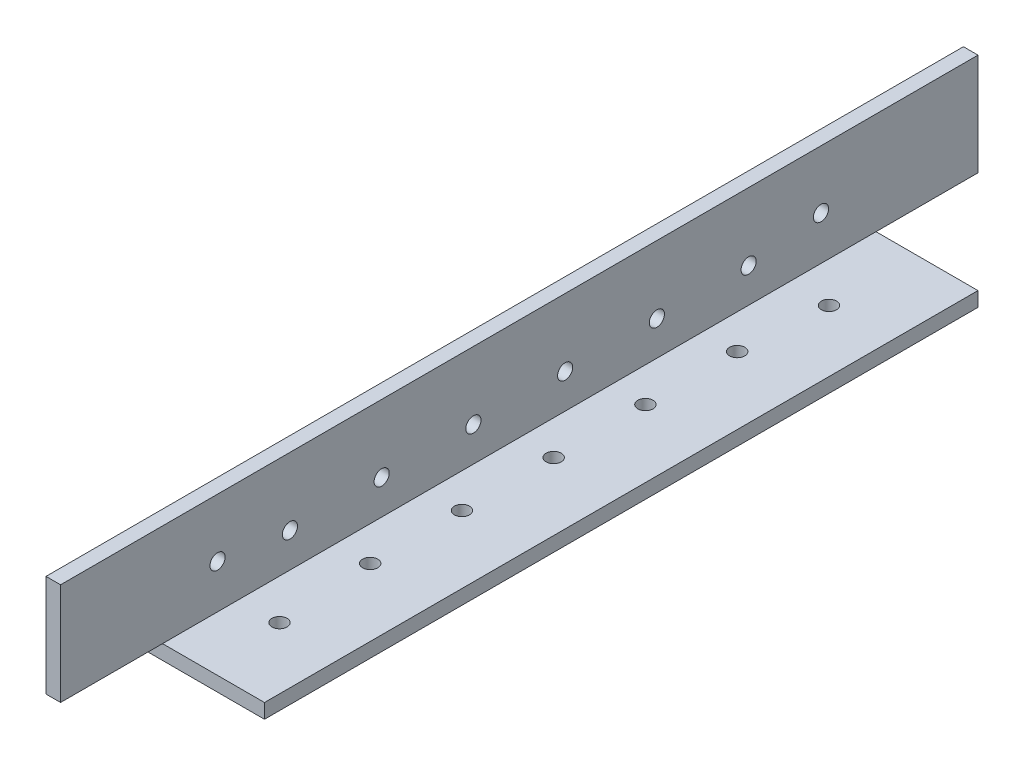
SolidWorks part; units mm, degrees
material "6061-T6 (SS)"
ref_plane "Front Plane" through (0, 0, 0) normal (0, 0, 1) x (1, 0, 0)
ref_plane "Top Plane" through (0, 0, 0) normal (0, 1, 0) x (1, 0, 0)
ref_plane "Right Plane" through (0, 0, 0) normal (1, 0, 0) x (0, 0, -1)
sketch "Sketch1" plane through (0, 0, 0) normal (0, 0, 1) x (1, 0, 0)
  line L0 (0, 25.4) -> (0, 0) construction
  line L1 (0, 0) -> (25.4, 0) construction
  line L2 (25.4, 0) -> (25.4, 3.175) construction
  line L3 (25.4, 3.175) -> (3.175, 3.175) construction
  line L4 (3.175, 3.175) -> (3.175, 25.4) construction
  line L6 (3.175, 25.4) -> (0, 25.4) construction
  arc A0 (3.175, 3.5814) -> (3.5814, 3.175) centre (3.5814, 3.5814) ccw construction
  point P4 (0, 0)
  dimension "Inside Corner Radius" = 0.4064
  dimension "Outside Height" = 25.4
  dimension "Inside Height" = 22.225
  dimension "Outside Width" = 25.4
  dimension "Inside Width" = 22.225
  dimension "Wall Thickness" = 3.175
  dimension "Shape" = 90
sketch "Sketch2" plane through (0, 0, 0) normal (1, 0, 0) x (0, 0, -1)
  line L0 (1219.2, 0) -> (-1219.2, 0) construction
  line L1 (-1219.2, 25.4) -> (-1219.2, 0) construction
  line L2 (1219.2, 25.4) -> (1219.2, 0) construction
  point P0 (-1189.99, 0)
  point P4 (0, 0)
  point P6 (1189.99, 0)
  dimension "D1" = 29.21
  dimension "D2" = 29.21
  dimension "D3" = 25.4
  dimension "Length" = 2438.4
sketch "Sketch3" plane through (0, 0, 0) normal (0, 0, 1) x (1, 0, 0)
  line L0 (3.175, 25.4) -> (0, 25.4)
  line L1 (0, 25.4) -> (0, 0)
  line L2 (0, 0) -> (25.4, 0)
  line L3 (25.4, 0) -> (25.4, 3.175)
  line L4 (25.4, 3.175) -> (3.175, 3.175)
  line L5 (3.175, 3.175) -> (3.175, 25.4)
extrude "Boss-Extrude1" add sketch "Sketch3" along normal mid plane 2438.4
fillet "Fillet1" radius 0.4064 1 edges at (3.175, 3.175, 0)
sketch "Sketch4" plane through (0, 0, 0) normal (-1, 0, 0) x (0, 0, 1)
  line L0 (1219.2, 25.4) -> (1219.2, 0) construction
  line L1 (-1219.2, 25.4) -> (1019.2, 25.4)
  line L2 (-1219.2, 25.4) -> (-1219.2, -77.8785)
  line L3 (-1219.2, -77.8785) -> (1019.2, -77.8785)
  line L4 (1019.2, 25.4) -> (1019.2, -77.8785)
  dimension "D1" = 200
extrude "Cut-Extrude1" cut sketch "Sketch4" against normal blind 60
sketch "Sketch5" plane through (0, 0, 0) normal (0, -1, 0) x (1, 0, 0)
  line L0 (0, 1219.2) -> (0, 1019.2) construction
  line L1 (25.4, 1019.2) -> (0, 1019.2)
  line L2 (25.4, 1019.2) -> (25.4, 1041.43)
  line L3 (25.4, 1041.43) -> (0, 1041.43)
  line L4 (0, 1019.2) -> (0, 1041.43)
  dimension "D1" = 22.23
extrude "Cut-Extrude2" cut sketch "Sketch5" against normal up to surface (3.175 mm away) up to face at (14.4907, 3.175, 1119.2)
sketch "Sketch6" plane through (0, 0, 0) normal (0, -1, 0) x (1, 0, 0)
  line L0 (0, 1219.2) -> (0, 1041.43) construction
  line L1 (25.4, 1219.2) -> (0, 1219.2)
  line L2 (25.4, 1219.2) -> (25.4, 1196.97)
  line L3 (25.4, 1196.97) -> (0, 1196.97)
  line L4 (0, 1219.2) -> (0, 1196.97)
  dimension "D1" = 22.23
extrude "Cut-Extrude3" cut sketch "Sketch6" against normal up to surface (3.175 mm away) up to face at (14.4907, 3.175, 1130.315)
sketch "Sketch7" plane through (0, 0, 1019.2) normal (0, 0, -1) x (-1, 0, 0)
  line L0 (-3.175, 3.5814) -> (-3.175, 25.4) construction
  line L1 (-3.175, 4.2) -> (-4.4439, 4.2)
  line L2 (-3.175, 4.2) -> (-3.175, 3.175)
  line L3 (-3.175, 3.175) -> (-4.4439, 3.175)
  line L4 (-4.4439, 4.2) -> (-4.4439, 3.175)
  line L5 (-3.5814, 3.175) -> (-25.4, 3.175) construction
extrude "Cut-Extrude4" cut sketch "Sketch7" against normal blind 220
sketch "Sketch9" plane through (3.175, 0, 0) normal (1, 0, 0) x (0, 0, -1)
  line L0 (-1219.2, 3.175) -> (-1219.2, 25.4) construction
  line L1 (-1196.97, 3.175) -> (-1041.43, 3.175) construction
  line L2 (-1019.2, 3.175) -> (-1019.2, 25.4) construction
  circle A0 centre (-1169.2, 10.675) radius 1.65
  circle A1 centre (-1149.2, 10.675) radius 1.65
  circle A2 centre (-1129.2, 10.675) radius 1.65
  circle A3 centre (-1109.2, 10.675) radius 1.65
  circle A4 centre (-1089.2, 10.675) radius 1.65
  circle A5 centre (-1069.2, 10.675) radius 1.65
  dimension "D1" = 50
  dimension "D2" = 7.5
  dimension "D3" = 3.3
  dimension "D5" = 50
  dimension "D4" = 6
extrude "Cut-Extrude5" cut sketch "Sketch9" against normal blind 20
sketch "Sketch10" plane through (0, 3.175, 0) normal (0, 1, 0) x (1, 0, 0)
  line L0 (600, -1019.2) -> (0, -1019.2) construction
  line L1 (3.175, -1196.97) -> (3.175, -1041.43) construction
  circle A0 centre (10.675, -1079.2) radius 1.65
  circle A1 centre (10.675, -1099.2) radius 1.65
  circle A2 centre (10.675, -1119.2) radius 1.65
  circle A3 centre (10.675, -1139.2) radius 1.65
  circle A4 centre (10.675, -1159.2) radius 1.65
  dimension "D1" = 60
  dimension "D2" = 7.5
  dimension "D3" = 3.3
  dimension "D5" = 20
  dimension "D4" = 5
extrude "Cut-Extrude6" cut sketch "Sketch10" against normal blind 20
sketch "Sketch11" plane through (3.175, 0, 0) normal (1, 0, 0) x (0, 0, -1)
  circle A0 centre (-1053.4257, 12.7) radius 1.65
  circle A1 centre (-1184.9793, 12.7) radius 1.65
  dimension "D1" = 3.3
extrude "Cut-Extrude7" cut sketch "Sketch11" against normal blind 70
sketch "Sketch12" plane through (0, 3.175, 0) normal (0, 1, 0) x (1, 0, 0)
  circle A0 centre (11.9634, -1180.2606) radius 1.65
  circle A1 centre (11.9634, -1060.48) radius 1.65
  dimension "D1" = 3.3
extrude "Cut-Extrude8" cut sketch "Sketch12" against normal blind 70
equation "\"D1@Boss-Extrude1\"=\"Length@Sketch2\""
equation "\"D1@Sketch2\" = \"Outside Width@Sketch1\" * 1.15"
equation "\"D2@Sketch2\"=\"D1@Sketch2\""
equation "\"D1@Fillet1\"=\"Inside Corner Radius@Sketch1\""
equation "\"D3@Sketch2\"=\"Outside Height@Sketch1\""
